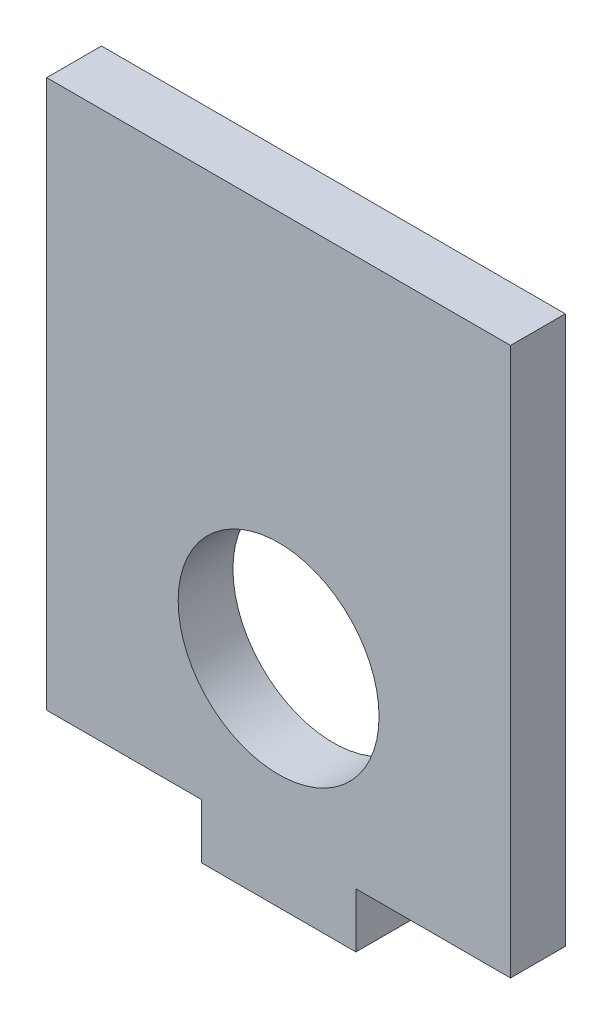
SolidWorks part; units mm, degrees
ref_plane "Front" through (0, 0, 0) normal (0, 0, 1) x (1, 0, 0)
ref_plane "Top" through (0, 0, 0) normal (0, 1, 0) x (1, 0, 0)
ref_plane "Right" through (0, 0, 0) normal (1, 0, 0) x (0, 0, -1)
sketch "Sketch1" plane through (0, 0, 0) normal (0, 0, 1) x (1, 0, 0)
  line L0 (-350.7169, 225.7985) -> (-350.7169, 285.7985)
  line L1 (-299.9169, 225.7985) -> (-299.9169, 285.7985)
  line L2 (-299.9169, 285.7985) -> (-350.7169, 285.7985)
  line L3 (-350.7169, 225.7985) -> (-333.7836, 225.7985)
  line L5 (-333.7836, 225.7985) -> (-333.7836, 219.7985)
  line L7 (-333.7836, 219.7985) -> (-316.8503, 219.7985)
  line L8 (-316.8503, 219.7985) -> (-316.8503, 225.7985)
  line L9 (-316.8503, 225.7985) -> (-299.9169, 225.7985)
  circle A0 centre (-325.3169, 243.3985) radius 11
  dimension "D4" = 22
  dimension "D1" = 60
  dimension "D2" = 16.9333
  dimension "D3" = 16.9333
extrude "Boss-Extrude1" add sketch "Sketch1" along normal blind 6
